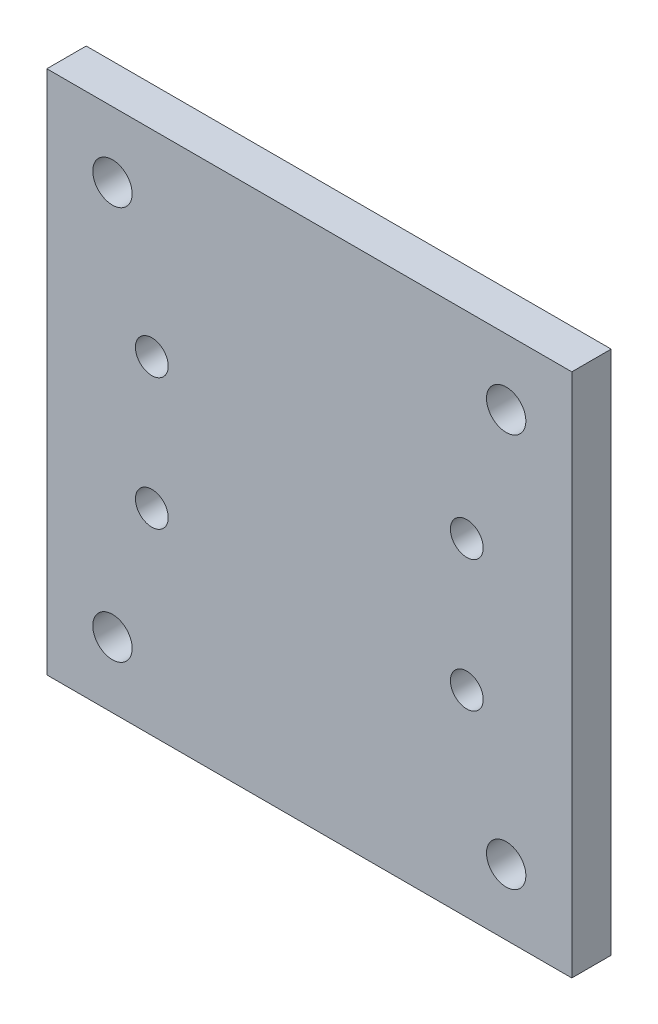
SolidWorks part; units mm, degrees
ref_plane "Plan de face" through (0, 0, 0) normal (0, 0, 1) x (1, 0, 0)
ref_plane "Plan de dessus" through (0, 0, 0) normal (0, 1, 0) x (1, 0, 0)
ref_plane "Plan de droite" through (0, 0, 0) normal (1, 0, 0) x (0, 0, -1)
sketch "Esquisse1" plane through (0, 0, 0) normal (0, 0, 1) x (1, 0, 0)
  line L0 (0, 20) -> (0, -20) construction
  line L1 (-20, -20) -> (20, -20)
  line L2 (-20, -20) -> (-20, 20)
  line L3 (-20, 20) -> (20, 20)
  line L4 (20, -20) -> (20, 20)
  line L5 (-20, -20) -> (20, 20) construction
  line L6 (-20, 20) -> (20, -20) construction
  line L8 (20, 0) -> (-20, 0) construction
  circle A0 centre (-15, 15) radius 1.5
  circle A1 centre (15, 15) radius 1.5
  circle A2 centre (15, -15) radius 1.5
  circle A3 centre (-15, -15) radius 1.5
  circle A4 centre (-12, 5) radius 1.25
  circle A5 centre (-12, -5) radius 1.25
  circle A6 centre (12, -5) radius 1.25
  circle A7 centre (12, 5) radius 1.25
  point P0 (0, 0)
  dimension "D4" = 15
  dimension "D5" = 3
  dimension "D6" = 12
  dimension "D7" = 2.5
  dimension "D1" = 40
  dimension "D2" = 40
  dimension "D3" = 15
  dimension "D8" = 5
extrude "Boss.-Extru.1" add sketch "Esquisse1" along normal blind 3
